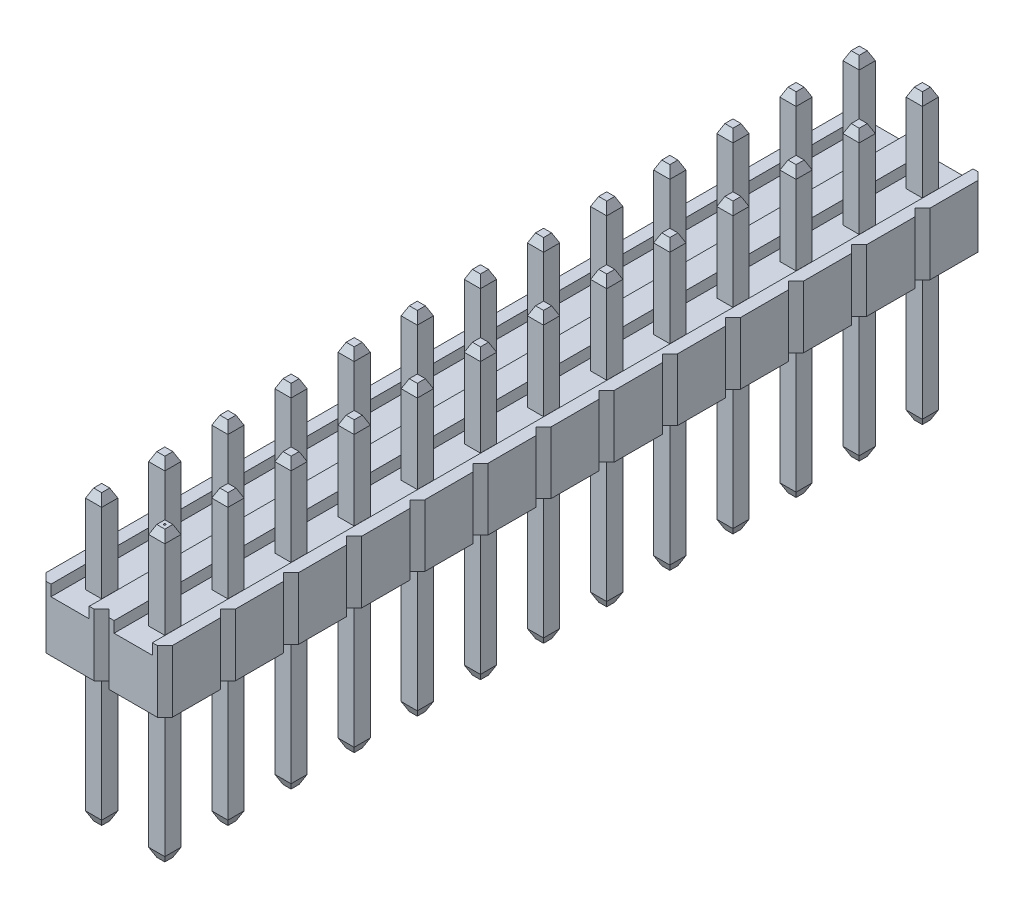
SolidWorks part; units mm, degrees
ref_plane "Front Plane" through (0, 0, 0) normal (0, 0, 1) x (1, 0, 0)
ref_plane "Top Plane" through (0, 0, 0) normal (0, 1, 0) x (1, 0, 0)
ref_plane "Right Plane" through (0, 0, 0) normal (1, 0, 0) x (0, 0, -1)
sketch "Sketch1" plane through (0, 0, 0) normal (0, 1, 0) x (1, 0, 0)
  line L0 (-0.97, 1.27) -> (0.97, 1.27)
  line L5 (0.97, 1.27) -> (1.27, 0.97)
  line L6 (1.27, 0.97) -> (1.27, -0.97)
  line L7 (1.27, -0.97) -> (0.97, -1.27)
  line L8 (0.97, -1.27) -> (-0.97, -1.27)
  line L9 (-0.97, -1.27) -> (-1.27, -0.97)
  line L10 (-1.27, -0.97) -> (-1.27, 0.97)
  line L11 (-1.27, 0.97) -> (-0.97, 1.27)
  dimension "D5" = 0.97
  dimension "D6" = 0.97
  dimension "D7" = 0.97
  dimension "D8" = 0.97
extrude "Extrude1" add sketch "Sketch1" along normal blind 2.5
sketch "Sketch2" plane through (0, 0, 1.27) normal (0, 0, 1) x (1, 0, 0)
  line L0 (-0.97, 0) -> (0.97, 0) construction
  line L1 (-0.77, 2.5687) -> (0.77, 2.5687)
  line L2 (-0.77, 2.5687) -> (-0.77, 2.06)
  line L3 (-0.77, 2.06) -> (0.77, 2.06)
  line L4 (0.77, 2.5687) -> (0.77, 2.06)
  dimension "D1" = 0.77
  dimension "D2" = 0.77
  dimension "D3" = 2.06
extrude "Cut-Extrude1" cut sketch "Sketch2" against normal blind 12.5
sketch "Sketch3" plane through (0, 2.06, 0) normal (0, 1, 0) x (-1, 0, 0)
  line L1 (0.325, -0.325) -> (-0.325, -0.325)
  line L2 (0.325, -0.325) -> (0.325, 0.325)
  line L3 (0.325, 0.325) -> (-0.325, 0.325)
  line L4 (-0.325, -0.325) -> (-0.325, 0.325)
  dimension "D1" = 0.65
  dimension "D2" = 0.325
  dimension "D3" = 0.65
  dimension "D4" = 0.325
extrude "Extrude2" add sketch "Sketch3" along normal blind 3.54
chamfer "Chamfer1" distance 0.35 angle 25 4 edges at (0, 5.6, -0.325) (0.325, 5.6, 0) (0, 5.6, 0.325) (-0.325, 5.6, 0)
sketch "Sketch4" plane through (0, 0, 0) normal (0, -1, 0) x (1, 0, 0)
  line L1 (-0.325, 0.325) -> (0.325, 0.325)
  line L2 (-0.325, 0.325) -> (-0.325, -0.325)
  line L3 (-0.325, -0.325) -> (0.325, -0.325)
  line L4 (0.325, 0.325) -> (0.325, -0.325)
extrude "Extrude3" add sketch "Sketch4" along normal blind 6
chamfer "Chamfer2" distance 0.35 angle 25 4 edges at (0, -6, 0.325) (0.325, -6, 0) (0, -6, -0.325) (-0.325, -6, 0)
pattern_linear "LPattern3" count 13 spacing 2.54 along (0, 0, -1) count 2 spacing 2.54 along (-1, 0, 0) of "Extrude1", "Cut-Extrude1"
pattern_linear "LPattern4" count 13 spacing 2.54 along (0, 0, -1) count 2 spacing 2.54 along (-1, 0, 0) of "Extrude2", "Chamfer1", "Extrude3", "Chamfer2"
sketch "Esboço1" plane through (0, 5.6, 0) normal (0, 1, 0) x (1, 0, 0)
  circle A0 centre (0, 0) radius 0.0396
extrude "Corte-extrusão1" cut sketch "Esboço1" against normal blind 0.1
